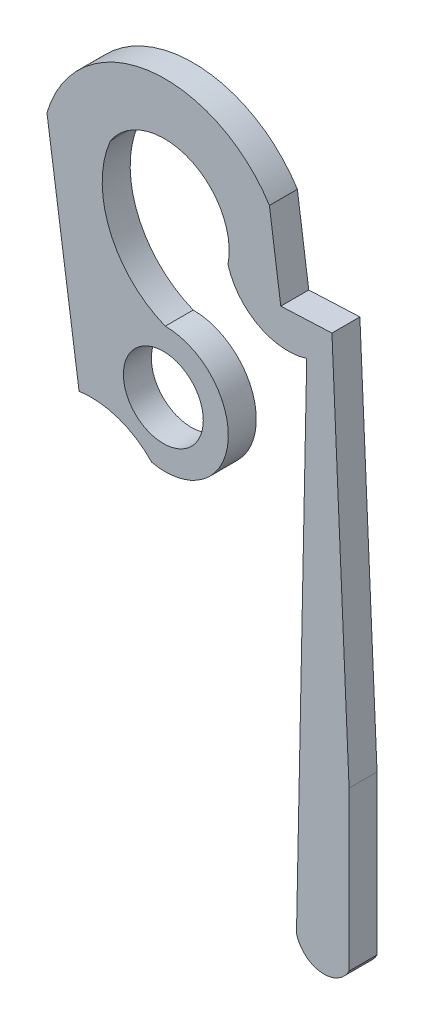
SolidWorks part; units mm, degrees
material "AISI 4340 Steel, normalized"
ref_plane "Front Plane" through (0, 0, 0) normal (0, 0, 1) x (1, 0, 0)
ref_plane "Top Plane" through (0, 0, 0) normal (0, 1, 0) x (1, 0, 0)
ref_plane "Right Plane" through (0, 0, 0) normal (1, 0, 0) x (0, 0, -1)
sketch "Sketch1" plane through (0, 0, 0) normal (0, 0, 1) x (1, 0, 0)
  line L0 (0.2144, 4.0365) -> (4.2844, 4.0365) construction
  line L1 (-33.8127, -4.8254) -> (30.8628, -4.8254) construction
  line L2 (-4.522, 7.997) -> (-3.5006, 0.8437)
  line L3 (2.5488, 8.9824) -> (2.9103, 6.3915)
  line L4 (2.9103, 6.3915) -> (4.5361, 6.4639)
  line L5 (4.5361, 6.4639) -> (5.0813, -5.7883)
  line L6 (5.0813, -10.8266) -> (5.0813, -5.7883)
  line L7 (3.7349, 5.3646) -> (3.4096, -10.6168)
  arc A0 (2.5488, 8.9824) -> (-4.522, 7.997) centre (-0.7646, 6.8965) ccw
  arc A1 (-3.5006, 0.8437) -> (-1.1894, 0.0409) centre (-3.1245, -1.8017) cw
  arc A2 (-1.1894, 0.0409) -> (-0.7619, 4.0047) centre (-0.7619, 1.9998) ccw
  arc A3 (-0.7619, 4.0047) -> (-2.5076, 8.2304) centre (0.4312, 6.971) cw
  arc A4 (-2.5076, 8.2304) -> (1.2324, 6.6973) centre (-0.7896, 7.0931) cw
  arc A5 (1.2324, 6.6973) -> (3.7349, 5.3646) centre (3.1347, 7.2534) ccw
  arc A6 (3.4096, -10.6168) -> (5.0813, -10.8266) centre (4.2844, -10.411) ccw
  circle A7 centre (-0.823, 2.0129) radius 1.27
  point P26 (4.2844, -10.411)
  dimension "D1" = 2.54
extrude "Boss-Extrude1" add sketch "Sketch1" along normal blind 0.889
